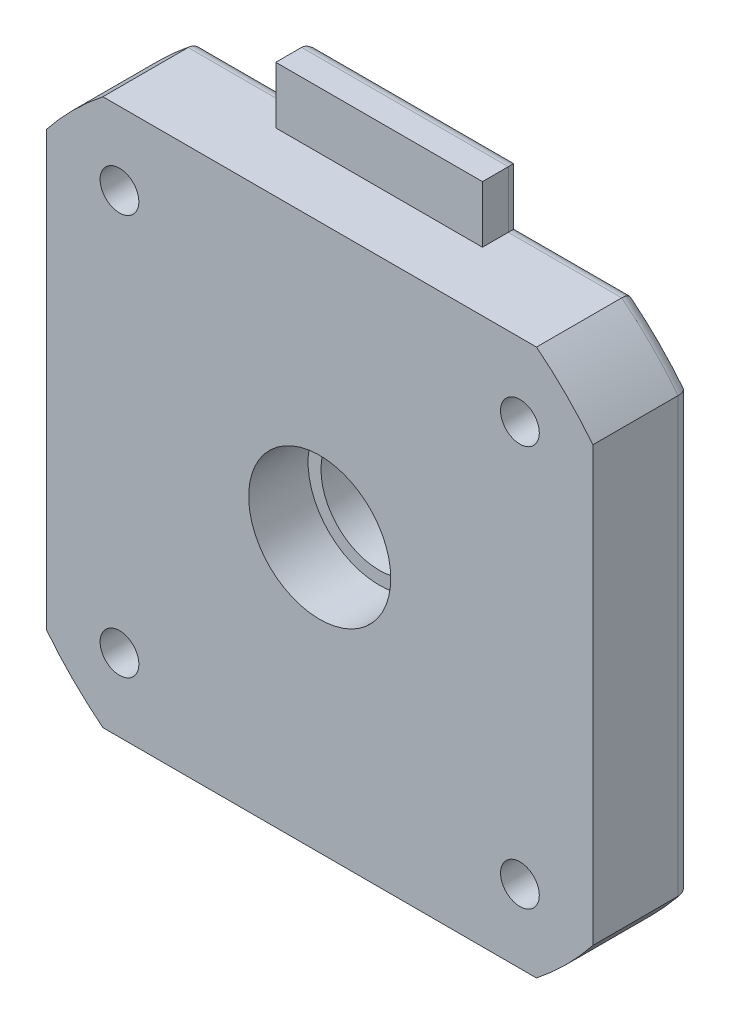
SolidWorks part; units mm, degrees
material "Acero aleado"
ref_plane "Alzado" through (0, 0, 0) normal (0, 0, 1) x (1, 0, 0)
ref_plane "Planta" through (0, 0, 0) normal (0, 1, 0) x (1, 0, 0)
ref_plane "Vista lateral" through (0, 0, 0) normal (1, 0, 0) x (0, 0, -1)
sketch "Croquis1" plane through (0, 0, 0) normal (0, 0, 1) x (1, 0, 0)
  line L0 (-21.15, 21.15) -> (21.15, 21.15)
  line L1 (-21.15, -21.15) -> (21.15, -21.15)
  line L2 (-21.15, 21.15) -> (-21.15, -21.15)
  line L4 (21.15, 21.15) -> (21.15, -21.15)
  line L5 (-21.15, 21.15) -> (21.15, -21.15) construction
  line L6 (-21.15, -21.15) -> (21.15, 21.15) construction
  point P0 (0, 0)
  point P6 (21.5586, -22.4082)
  dimension "D1" = 42.3
  dimension "D2" = 42.3
extrude "Extrude Feature" add sketch "Croquis1" along normal blind 7.6
sketch "Sketch2" plane through (0, 0, 7.6) normal (0, 0, 1) x (1, 0, 0)
  circle A0 centre (0, 0) radius 27
  circle A1 centre (0, 0) radius 29.9106
  dimension "D1" = 54
extrude "Cut-Extrude1" cut sketch "Sketch2" against normal through all
sketch "Croquis5" plane through (0, 0, 0) normal (0, 0, -1) x (-1, 0, 0)
  circle A0 centre (-15.5, 15.5) radius 1.5
  circle A1 centre (15.5, 15.5) radius 1.5
  circle A2 centre (15.5, -15.5) radius 1.5
  circle A3 centre (-15.5, -15.5) radius 1.5
  point P12 (0, 0)
  dimension "D1" = 3
  dimension "D2" = 15.5
  dimension "D3" = 15.5
  dimension "D5" = 31
  dimension "D6" = 15.5
  dimension "D4" = 4
extrude "Cortar-Extruir2" cut sketch "Croquis5" against normal blind 22
sketch "Croquis6" plane through (0, 0, 0) normal (0, 0, -1) x (-1, 0, 0)
  circle A0 centre (0, 0) radius 4.5
  dimension "D1" = 9
extrude "Cortar-Extruir3" cut sketch "Croquis6" against normal through all
sketch "Sketch3" plane through (0, 0, 7.6) normal (0, 0, 1) x (1, 0, 0)
  circle A0 centre (0, 0) radius 5.5
  point P2 (0, 0)
  dimension "D1" = 11
extrude "Cut-Extrude2" cut sketch "Sketch3" against normal offset from surface (4.6 mm away) 3 up to face at (-4.5, 0, 0)
sketch "Croquis7" plane through (0, 0, 0) normal (0, 0, -1) x (-1, 0, 0)
  circle A0 centre (-15.5, 15.5) radius 3
  circle A1 centre (15.5, 15.5) radius 3
  circle A2 centre (15.5, -15.5) radius 3
  circle A3 centre (-15.5, -15.5) radius 3
  point P4 (-15.5, -15.5)
  dimension "D1" = 6
  dimension "D2" = 4
extrude "Cortar-Extruir4" cut sketch "Croquis7" against normal blind 3
sketch "Sketch1" plane through (0, 0, 0) normal (0, 0, -1) x (-1, 0, 0)
  line L1 (-8, 25.55) -> (8, 25.55)
  line L2 (-8, 25.55) -> (-8, 21.15)
  line L3 (-8, 21.15) -> (8, 21.15)
  line L4 (8, 25.55) -> (8, 21.15)
  line L5 (-8, 25.55) -> (8, 21.15) construction
  line L6 (-8, 21.15) -> (8, 25.55) construction
  line L7 (-16.7833, 21.15) -> (16.7833, 21.15) construction
  point P0 (0, 23.35)
  point P5 (8, 21.15)
  point P7 (0, 0)
  point P9 (0, 0)
  dimension "D1" = 16
  dimension "D2" = 4.4
extrude "Boss-Extrude1" add sketch "Sketch1" against normal blind 3
fillet "Fillet1" radius 1 12 edges at (-19.0919, 19.0919, 0) (-21.15, 0, 0) (-19.0919, -19.0919, 0) (0, -21.15, 0) (19.0919, -19.0919, 0) (21.15, 0, 0) (19.0919, 19.0919, 0) (-8, 23.35, 0) (0, 25.55, 0) (-12.3916, 21.15, 0) (8, 23.35, 0) (12.3916, 21.15, 0)
chamfer "Chamfer1" distance 0.5 angle 45 4 edges at (-18.5, -15.5, 0) (12.5, -15.5, 0) (-18.5, 15.5, 0) (12.5, 15.5, 0)
